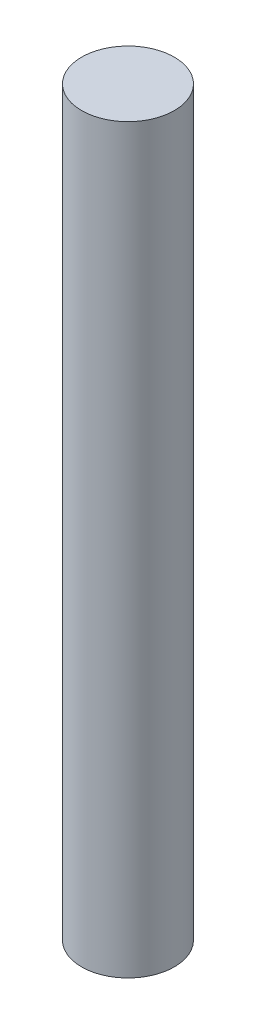
SolidWorks part; units mm, degrees
ref_plane "Front" through (0, 0, 0) normal (0, 0, 1) x (1, 0, 0)
ref_plane "Top" through (0, 0, 0) normal (0, 1, 0) x (1, 0, 0)
ref_plane "Right" through (0, 0, 0) normal (1, 0, 0) x (0, 0, -1)
sketch "Sketch1" plane through (0, 0, 0) normal (0, 1, 0) x (1, 0, 0)
  circle A0 centre (0, 0) radius 9.525
extrude "Boss-Extrude1" add sketch "Sketch1" along normal blind 152.4
